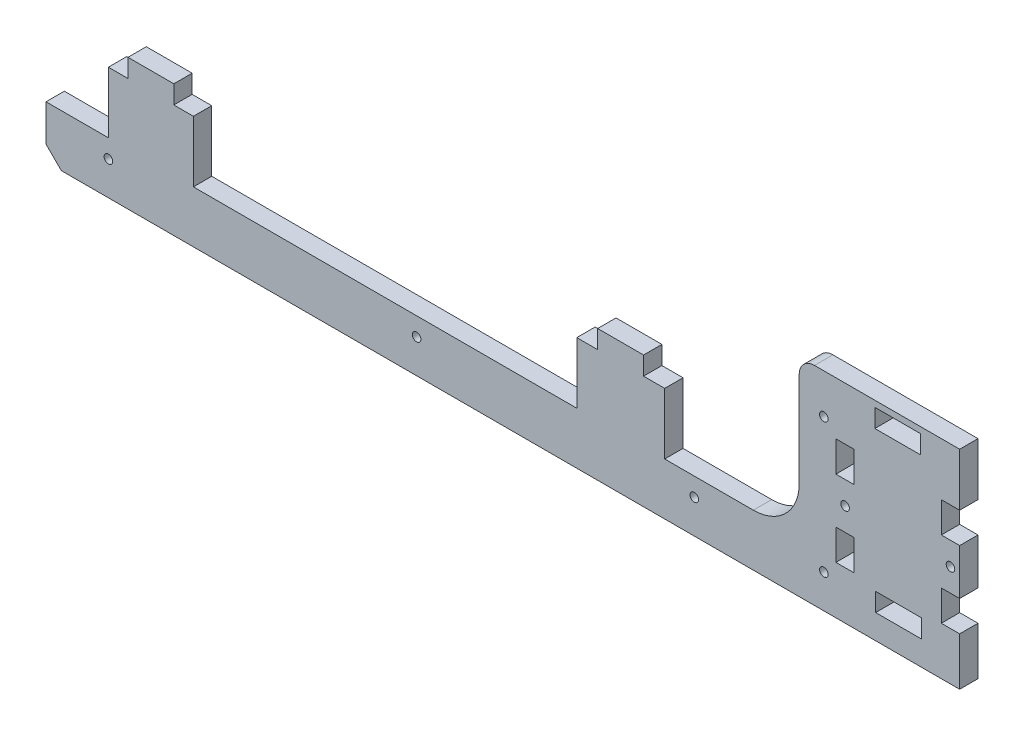
SolidWorks part; units mm, degrees
ref_plane "Front" through (0, 0, 0) normal (0, 0, 1) x (1, 0, 0)
ref_plane "Top" through (0, 0, 0) normal (0, 1, 0) x (1, 0, 0)
ref_plane "Right" through (0, 0, 0) normal (1, 0, 0) x (0, 0, -1)
sketch "Эскиз1" plane through (0, 0, 0) normal (0, 0, 1) x (1, 0, 0)
  line L46 (96.9208, 2) -> (96.9208, 25)
  line L55 (149.3892, 30) -> (149.3892, 20.7093)
  line L56 (149.3892, -30) -> (-144.3892, -30)
  line L57 (-144.3892, -30) -> (-149.3892, -25)
  line L58 (-149.3892, -25) -> (-149.3892, -13)
  line L59 (81.9208, -13) -> (52.9291, -13)
  line L72 (121.9208, -16) -> (136.9208, -16)
  line L73 (121.9208, -16) -> (121.9208, -22)
  line L74 (121.9208, -22) -> (136.9208, -22)
  line L75 (136.9208, -16) -> (136.9208, -22)
  line L76 (143.3892, 20.7093) -> (149.3892, 20.7093)
  line L77 (143.3892, 20.7093) -> (143.3892, 10.7093)
  line L78 (143.3892, 10.7093) -> (149.3892, 10.7093)
  line L80 (143.3892, -4.2907) -> (149.3892, -4.2907)
  line L81 (143.3892, -4.2907) -> (143.3892, -14.2907)
  line L82 (143.3892, -14.2907) -> (149.3892, -14.2907)
  line L84 (108.9208, 20.7093) -> (114.9208, 20.7093)
  line L85 (108.9208, 20.7093) -> (108.9208, 10.7093)
  line L86 (108.9208, 10.7093) -> (114.9208, 10.7093)
  line L87 (114.9208, 20.7093) -> (114.9208, 10.7093)
  line L88 (108.9208, -14.2907) -> (114.9208, -14.2907)
  line L89 (108.9208, -14.2907) -> (108.9208, -4.2907)
  line L90 (108.9208, -4.2907) -> (114.9208, -4.2907)
  line L91 (114.9208, -14.2907) -> (114.9208, -4.2907)
  line L99 (-135.3886, -19) -> (69.0114, -19) construction
  line L105 (149.3892, 10.7093) -> (149.3892, -4.2907)
  line L106 (149.3892, -14.2907) -> (149.3892, -30)
  line L107 (111.9208, 10.7093) -> (111.9208, -4.2907) construction
  line L108 (146.3892, 10.7093) -> (146.3892, -4.2907) construction
  line L109 (108.9208, 3.2093) -> (149.3892, 3.2405) construction
  line L110 (-128.9886, -2.5796) -> (-128.9886, -38.6586) construction
  line L119 (-28.1886, -6.9168) -> (-28.1886, -36.2533) construction
  line L120 (62.6114, -5.7851) -> (62.6114, -36.2533) construction
  line L121 (-8.1886, -19) -> (-8.1886, -38.6586) construction
  line L126 (-128.9886, -13) -> (-149.3892, -13)
  line L131 (24.179, -13) -> (-101.1886, -13)
  line L133 (149.3892, 30) -> (149.3892, 38)
  line L134 (149.3892, 38) -> (101.9208, 38)
  line L135 (96.9208, 33) -> (96.9208, 25)
  line L136 (-149.3892, 7) -> (96.9208, 7) construction
  line L137 (121.6558, 36) -> (136.6558, 36)
  line L138 (121.6558, 36) -> (121.6558, 30)
  line L139 (121.6558, 30) -> (136.6558, 30)
  line L140 (136.6558, 36) -> (136.6558, 30)
  line L141 (-122.5886, 20.7093) -> (-122.5886, 7) construction
  line L142 (31.0214, 20.7093) -> (31.0214, 7) construction
  line L143 (-149.3892, 13) -> (85.2625, 13) construction
  line L144 (-101.1886, 7) -> (-101.1886, -13)
  line L145 (-122.5886, 13) -> (-107.5886, 13)
  line L146 (-122.5886, 13) -> (-122.5886, 7)
  line L148 (-107.5886, 13) -> (-107.5886, 7)
  line L149 (31.0214, 13) -> (46.0214, 13)
  line L150 (31.0214, 13) -> (31.0214, 7)
  line L152 (46.0214, 13) -> (46.0214, 7)
  line L153 (-128.9886, 7) -> (-122.5886, 7)
  line L154 (-128.9886, 7) -> (-128.9886, -13)
  line L157 (-107.5886, 7) -> (-101.1886, 7)
  line L158 (46.0214, 7) -> (52.9291, 7)
  line L159 (24.179, 7) -> (31.0214, 7)
  line L160 (24.179, 7) -> (24.179, -13)
  line L162 (52.9291, 7) -> (52.9291, -13)
  arc A6 (96.9208, 2) -> (81.9208, -13) centre (81.9208, 2) cw
  circle A8 centre (104.9708, -19) radius 1.4
  circle A9 centre (104.9708, 25) radius 1.4
  circle A10 centre (111.9208, 3.2093) radius 1.4
  circle A11 centre (146.3892, 3.2093) radius 1.4
  circle A12 centre (-128.9886, -19) radius 1.4
  circle A13 centre (-28.1886, -19) radius 1.4
  circle A14 centre (62.6114, -19) radius 1.4
  arc A15 (101.9208, 38) -> (96.9208, 33) centre (101.9208, 33) ccw
  dimension "D1" = 2.8
  dimension "D2" = 2.8
  dimension "D3" = 2.8
  dimension "D5" = 2.8
  dimension "D6" = 2.8
  dimension "D8" = 50.8994
  dimension "D13" = 5
  dimension "D4" = 20
  dimension "D7" = 43.9917
  dimension "D9" = 8
  dimension "D10" = 2
  dimension "D11" = 15
  dimension "D12" = 6
  dimension "D14" = 20
  dimension "D15" = 6
  dimension "D16" = 65.8994
  dimension "D17" = 72.7418
extrude "Бобышка-Вытянуть1" add sketch "Эскиз1" along normal blind 6
